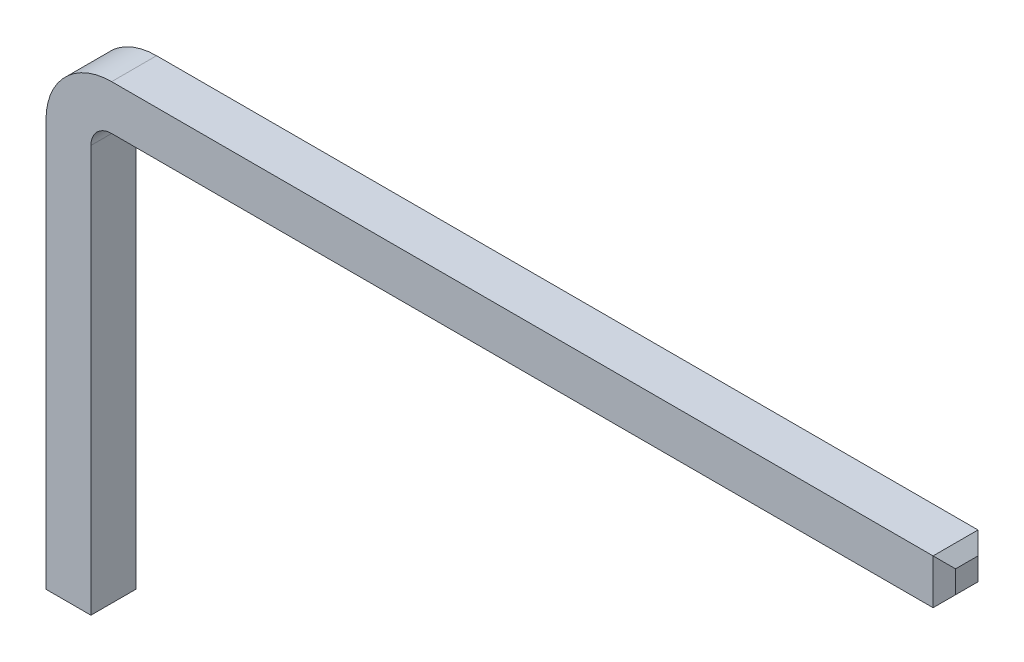
SolidWorks part; units mm, degrees
ref_plane "Front" through (0, 0, 0) normal (0, 0, 1) x (1, 0, 0)
ref_plane "Top" through (0, 0, 0) normal (0, 1, 0) x (1, 0, 0)
ref_plane "Right" through (0, 0, 0) normal (1, 0, 0) x (0, 0, -1)
sketch "Sketch1" plane through (0, 0, 0) normal (0, 0, 1) x (1, 0, 0)
  line L0 (0.95, 7) -> (13, 7)
  line L1 (0, 6.05) -> (0, 0)
  line L2 (13, 7) -> (13, 6.35)
  line L3 (0, 0) -> (0.65, 0)
  line L4 (0.65, 0) -> (0.65, 6.05)
  line L5 (0.95, 6.35) -> (13, 6.35)
  arc A0 (0.65, 6.05) -> (0.95, 6.35) centre (0.95, 6.05) cw
  arc A1 (0, 6.05) -> (0.95, 7) centre (0.95, 6.05) cw
extrude "Body" add sketch "Sketch1" along normal blind 0.65
chamfer "Chamfer" distance 0.1625 angle 45
